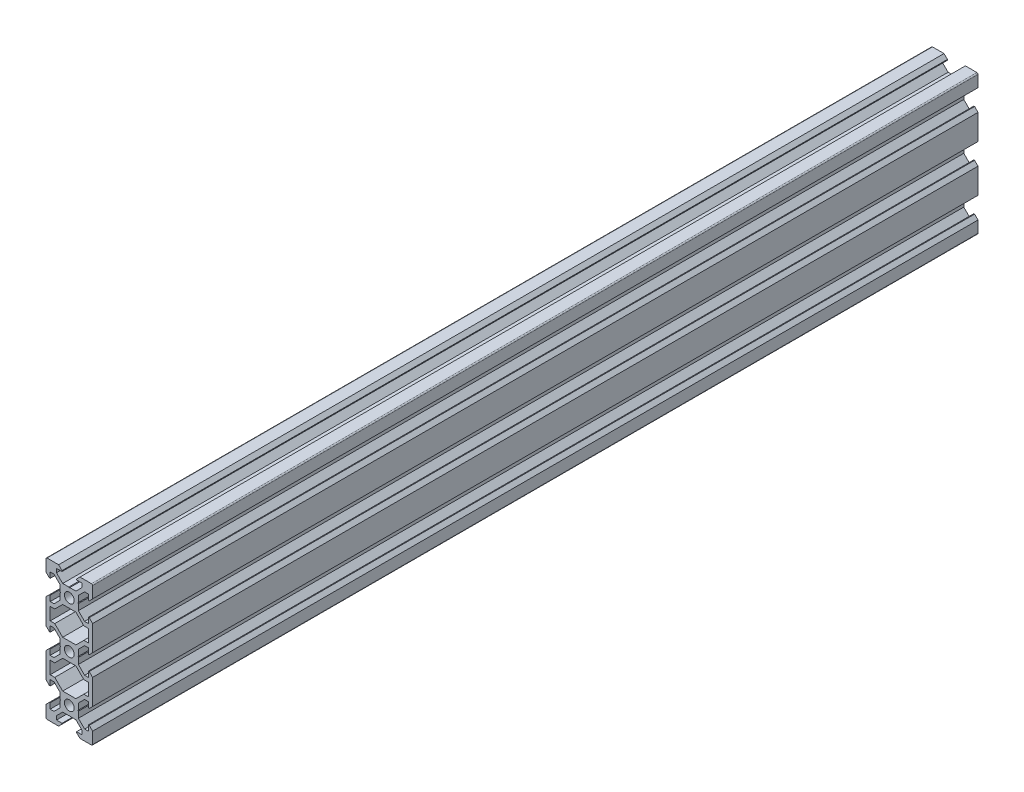
SolidWorks part; units mm, degrees
material "6061-T6 (SS)"
ref_plane "Front Plane" through (0, 0, 0) normal (0, 0, 1) x (1, 0, 0)
ref_plane "Top Plane" through (0, 0, 0) normal (0, 1, 0) x (1, 0, 0)
ref_plane "Right Plane" through (0, 0, 0) normal (1, 0, 0) x (0, 0, -1)
sketch "Sketch1" plane through (0, 0, 0) normal (0, 0, 1) x (1, 0, 0)
  line L0 (0, 0) -> (10, 0) construction
  line L1 (9.5, -30) -> (-9.5, -30)
  line L2 (10, -29.5) -> (10, 29.5)
  line L3 (9.5, 30) -> (-9.5, 30)
  line L4 (-10, -29.5) -> (-10, 29.5)
  line L5 (10, -30) -> (-10, 30) construction
  line L6 (10, 30) -> (-10, -30) construction
  circle A0 centre (0, 20) radius 2.1
  circle A1 centre (0, 0) radius 2.1
  circle A2 centre (0, -20) radius 2.1
  arc A3 (-9.5, -30) -> (-10, -29.5) centre (-9.5, -29.5) cw
  arc A4 (9.5, -30) -> (10, -29.5) centre (9.5, -29.5) ccw
  arc A5 (10, 29.5) -> (9.5, 30) centre (9.5, 29.5) ccw
  arc A6 (-9.5, 30) -> (-10, 29.5) centre (-9.5, 29.5) ccw
  point P0 (0, 0)
  line B0 (0, 20) -> (0, 30) construction
  line B1 (0, 23.69) -> (-0.21, 23.9)
  line B2 (-0.21, 23.9) -> (-2.8393, 23.9)
  line B3 (-2.8393, 23.9) -> (-5.5, 26.5607)
  line B4 (-5.5, 26.5607) -> (-5.5, 28.2)
  line B5 (-5.5, 28.2) -> (-3.125, 28.2)
  line B6 (-3.125, 28.2) -> (-3.125, 28.545)
  line B7 (-3.125, 28.545) -> (-4.58, 30)
  line B8 (-4.58, 30) -> (4.58, 30)
  line B9 (0, 20) -> (-5.9132, 25.9132) construction
  line B10 (3.125, 28.545) -> (4.58, 30)
  line B11 (3.125, 28.2) -> (3.125, 28.545)
  line B12 (5.5, 28.2) -> (3.125, 28.2)
  line B13 (5.5, 26.5607) -> (5.5, 28.2)
  line B14 (2.8393, 23.9) -> (5.5, 26.5607)
  line B15 (0.21, 23.9) -> (2.8393, 23.9)
  line B16 (0, 23.69) -> (0.21, 23.9)
  line B17 (0, 20) -> (-10, 20) construction
  line B18 (-3.69, 20) -> (-3.9, 19.79)
  line B19 (-3.9, 19.79) -> (-3.9, 17.1607)
  line B20 (-3.9, 17.1607) -> (-6.5607, 14.5)
  line B21 (-6.5607, 14.5) -> (-8.2, 14.5)
  line B22 (-8.2, 14.5) -> (-8.2, 16.875)
  line B23 (-8.2, 16.875) -> (-8.545, 16.875)
  line B24 (-8.545, 16.875) -> (-10, 15.42)
  line B25 (-10, 15.42) -> (-10, 24.58)
  line B26 (0, 20) -> (-5.9132, 14.0868) construction
  line B27 (-8.545, 23.125) -> (-10, 24.58)
  line B28 (-8.2, 23.125) -> (-8.545, 23.125)
  line B29 (-8.2, 25.5) -> (-8.2, 23.125)
  line B30 (-6.5607, 25.5) -> (-8.2, 25.5)
  line B31 (-3.9, 22.8393) -> (-6.5607, 25.5)
  line B32 (-3.9, 20.21) -> (-3.9, 22.8393)
  line B33 (-3.69, 20) -> (-3.9, 20.21)
  line B34 (0, 0) -> (-10, 0) construction
  line B35 (-3.69, 0) -> (-3.9, -0.21)
  line B36 (-3.9, -0.21) -> (-3.9, -2.8393)
  line B37 (-3.9, -2.8393) -> (-6.5607, -5.5)
  line B38 (-6.5607, -5.5) -> (-8.2, -5.5)
  line B39 (-8.2, -5.5) -> (-8.2, -3.125)
  line B40 (-8.2, -3.125) -> (-8.545, -3.125)
  line B41 (-8.545, -3.125) -> (-10, -4.58)
  line B42 (-10, -4.58) -> (-10, 4.58)
  line B43 (0, 0) -> (-5.9132, -5.9132) construction
  line B44 (-8.545, 3.125) -> (-10, 4.58)
  line B45 (-8.2, 3.125) -> (-8.545, 3.125)
  line B46 (-8.2, 5.5) -> (-8.2, 3.125)
  line B47 (-6.5607, 5.5) -> (-8.2, 5.5)
  line B48 (-3.9, 2.8393) -> (-6.5607, 5.5)
  line B49 (-3.9, 0.21) -> (-3.9, 2.8393)
  line B50 (-3.69, 0) -> (-3.9, 0.21)
  line B51 (0, -20) -> (-10, -20) construction
  line B52 (-3.69, -20) -> (-3.9, -20.21)
  line B53 (-3.9, -20.21) -> (-3.9, -22.8393)
  line B54 (-3.9, -22.8393) -> (-6.5607, -25.5)
  line B55 (-6.5607, -25.5) -> (-8.2, -25.5)
  line B56 (-8.2, -25.5) -> (-8.2, -23.125)
  line B57 (-8.2, -23.125) -> (-8.545, -23.125)
  line B58 (-8.545, -23.125) -> (-10, -24.58)
  line B59 (-10, -24.58) -> (-10, -15.42)
  line B60 (0, -20) -> (-5.9132, -25.9132) construction
  line B61 (-8.545, -16.875) -> (-10, -15.42)
  line B62 (-8.2, -16.875) -> (-8.545, -16.875)
  line B63 (-8.2, -14.5) -> (-8.2, -16.875)
  line B64 (-6.5607, -14.5) -> (-8.2, -14.5)
  line B65 (-3.9, -17.1607) -> (-6.5607, -14.5)
  line B66 (-3.9, -19.79) -> (-3.9, -17.1607)
  line B67 (-3.69, -20) -> (-3.9, -19.79)
  line B68 (0, -20) -> (0, -30) construction
  line B69 (0, -23.69) -> (0.21, -23.9)
  line B70 (0.21, -23.9) -> (2.8393, -23.9)
  line B71 (2.8393, -23.9) -> (5.5, -26.5607)
  line B72 (5.5, -26.5607) -> (5.5, -28.2)
  line B73 (5.5, -28.2) -> (3.125, -28.2)
  line B74 (3.125, -28.2) -> (3.125, -28.545)
  line B75 (3.125, -28.545) -> (4.58, -30)
  line B76 (4.58, -30) -> (-4.58, -30)
  line B77 (0, -20) -> (5.9132, -25.9132) construction
  line B78 (-3.125, -28.545) -> (-4.58, -30)
  line B79 (-3.125, -28.2) -> (-3.125, -28.545)
  line B80 (-5.5, -28.2) -> (-3.125, -28.2)
  line B81 (-5.5, -26.5607) -> (-5.5, -28.2)
  line B82 (-2.8393, -23.9) -> (-5.5, -26.5607)
  line B83 (-0.21, -23.9) -> (-2.8393, -23.9)
  line B84 (0, -23.69) -> (-0.21, -23.9)
  line B85 (0, -20) -> (10, -20) construction
  line B86 (3.69, -20) -> (3.9, -19.79)
  line B87 (3.9, -19.79) -> (3.9, -17.1607)
  line B88 (3.9, -17.1607) -> (6.5607, -14.5)
  line B89 (6.5607, -14.5) -> (8.2, -14.5)
  line B90 (8.2, -14.5) -> (8.2, -16.875)
  line B91 (8.2, -16.875) -> (8.545, -16.875)
  line B92 (8.545, -16.875) -> (10, -15.42)
  line B93 (10, -15.42) -> (10, -24.58)
  line B94 (0, -20) -> (5.9132, -14.0868) construction
  line B95 (8.545, -23.125) -> (10, -24.58)
  line B96 (8.2, -23.125) -> (8.545, -23.125)
  line B97 (8.2, -25.5) -> (8.2, -23.125)
  line B98 (6.5607, -25.5) -> (8.2, -25.5)
  line B99 (3.9, -22.8393) -> (6.5607, -25.5)
  line B100 (3.9, -20.21) -> (3.9, -22.8393)
  line B101 (3.69, -20) -> (3.9, -20.21)
  line B102 (0, 0) -> (10, 0) construction
  line B103 (3.69, 0) -> (3.9, 0.21)
  line B104 (3.9, 0.21) -> (3.9, 2.8393)
  line B105 (3.9, 2.8393) -> (6.5607, 5.5)
  line B106 (6.5607, 5.5) -> (8.2, 5.5)
  line B107 (8.2, 5.5) -> (8.2, 3.125)
  line B108 (8.2, 3.125) -> (8.545, 3.125)
  line B109 (8.545, 3.125) -> (10, 4.58)
  line B110 (10, 4.58) -> (10, -4.58)
  line B111 (0, 0) -> (5.9132, 5.9132) construction
  line B112 (8.545, -3.125) -> (10, -4.58)
  line B113 (8.2, -3.125) -> (8.545, -3.125)
  line B114 (8.2, -5.5) -> (8.2, -3.125)
  line B115 (6.5607, -5.5) -> (8.2, -5.5)
  line B116 (3.9, -2.8393) -> (6.5607, -5.5)
  line B117 (3.9, -0.21) -> (3.9, -2.8393)
  line B118 (3.69, 0) -> (3.9, -0.21)
  line B119 (0, 20) -> (10, 20) construction
  line B120 (3.69, 20) -> (3.9, 20.21)
  line B121 (3.9, 20.21) -> (3.9, 22.8393)
  line B122 (3.9, 22.8393) -> (6.5607, 25.5)
  line B123 (6.5607, 25.5) -> (8.2, 25.5)
  line B124 (8.2, 25.5) -> (8.2, 23.125)
  line B125 (8.2, 23.125) -> (8.545, 23.125)
  line B126 (8.545, 23.125) -> (10, 24.58)
  line B127 (10, 24.58) -> (10, 15.42)
  line B128 (0, 20) -> (5.9132, 25.9132) construction
  line B129 (8.545, 16.875) -> (10, 15.42)
  line B130 (8.2, 16.875) -> (8.545, 16.875)
  line B131 (8.2, 14.5) -> (8.2, 16.875)
  line B132 (6.5607, 14.5) -> (8.2, 14.5)
  line B133 (3.9, 17.1607) -> (6.5607, 14.5)
  line B134 (3.9, 19.79) -> (3.9, 17.1607)
  line B135 (3.69, 20) -> (3.9, 19.79)
  line B136 (-8.2, 7.3) -> (-8.2, 12.7)
  line B137 (-8.2, 12.7) -> (-6.2393, 12.7)
  line B138 (-6.2393, 12.7) -> (-2.8393, 16.1)
  line B139 (-2.8393, 16.1) -> (2.8393, 16.1)
  line B140 (0, 16.1) -> (0, 10) construction
  line B141 (0, 10) -> (-8.2, 10) construction
  line B142 (6.2393, 12.7) -> (2.8393, 16.1)
  line B143 (8.2, 12.7) -> (6.2393, 12.7)
  line B144 (8.2, 7.3) -> (8.2, 12.7)
  line B145 (8.2, 7.3) -> (6.2393, 7.3)
  line B146 (6.2393, 7.3) -> (2.8393, 3.9)
  line B147 (-2.8393, 3.9) -> (2.8393, 3.9)
  line B148 (-6.2393, 7.3) -> (-2.8393, 3.9)
  line B149 (-8.2, 7.3) -> (-6.2393, 7.3)
  line B150 (0, 16.1) -> (0, 20) construction
  line B151 (0, 20) -> (-5.0927, 14.9073) construction
  line B152 (-8.2, -12.7) -> (-8.2, -7.3)
  line B153 (-8.2, -7.3) -> (-6.2393, -7.3)
  line B154 (-6.2393, -7.3) -> (-2.8393, -3.9)
  line B155 (-2.8393, -3.9) -> (2.8393, -3.9)
  line B156 (0, -3.9) -> (0, -10) construction
  line B157 (0, -10) -> (-8.2, -10) construction
  line B158 (6.2393, -7.3) -> (2.8393, -3.9)
  line B159 (8.2, -7.3) -> (6.2393, -7.3)
  line B160 (8.2, -12.7) -> (8.2, -7.3)
  line B161 (8.2, -12.7) -> (6.2393, -12.7)
  line B162 (6.2393, -12.7) -> (2.8393, -16.1)
  line B163 (-2.8393, -16.1) -> (2.8393, -16.1)
  line B164 (-6.2393, -12.7) -> (-2.8393, -16.1)
  line B165 (-8.2, -12.7) -> (-6.2393, -12.7)
  line B166 (0, -3.9) -> (0, 0) construction
  line B167 (0, 0) -> (-5.0927, -5.0927) construction
  dimension "D3" = 4.2
  dimension "D5" = 0.5
  dimension "D1" = 20
  dimension "D2" = 60
  dimension "D4" = 40
sketch_block_instance "V Slot 1-4"
sketch_block "V Slot 1" parameters "D1"=10, "D2"=11, "D3"=4.3, "D4"=1.8, "D5"=0.21, "D6"=45, "D7"=9.16, "D8"=1.5, "D9"=6.25
sketch_block_instance "V Slot 1-5"
sketch_block_instance "V Slot 1-6"
sketch_block_instance "V Slot 1-7"
sketch_block_instance "V Slot 1-8"
sketch_block_instance "V Slot 1-9"
sketch_block_instance "V Slot 1-10"
sketch_block_instance "V Slot 1-11"
sketch_block_instance "Center Cutout 1-1"
sketch_block "Center Cutout 1" parameters "D1"=5.4, "D2"=12.2, "D3"=8.2, "D4"=45, "D5"=10, "D6"=1.5
sketch_block_instance "Center Cutout 1-2"
extrude "Boss-Extrude1" add sketch "Sketch1" along normal blind 380 contours B135 B120 B121 B122 B123 B124 B125 B126 L2 A5 L3 B10 B11 B12 B13 B14 B15 B16 B1 B2 B3 B4 B5 B6 B7 A6 L4 B27 B28 B29 B30 B31 B32 B33 B18 B19 B20 B21 B22 B23 B24 B44 B45 B46 B47 B48 B49 B50 B35
